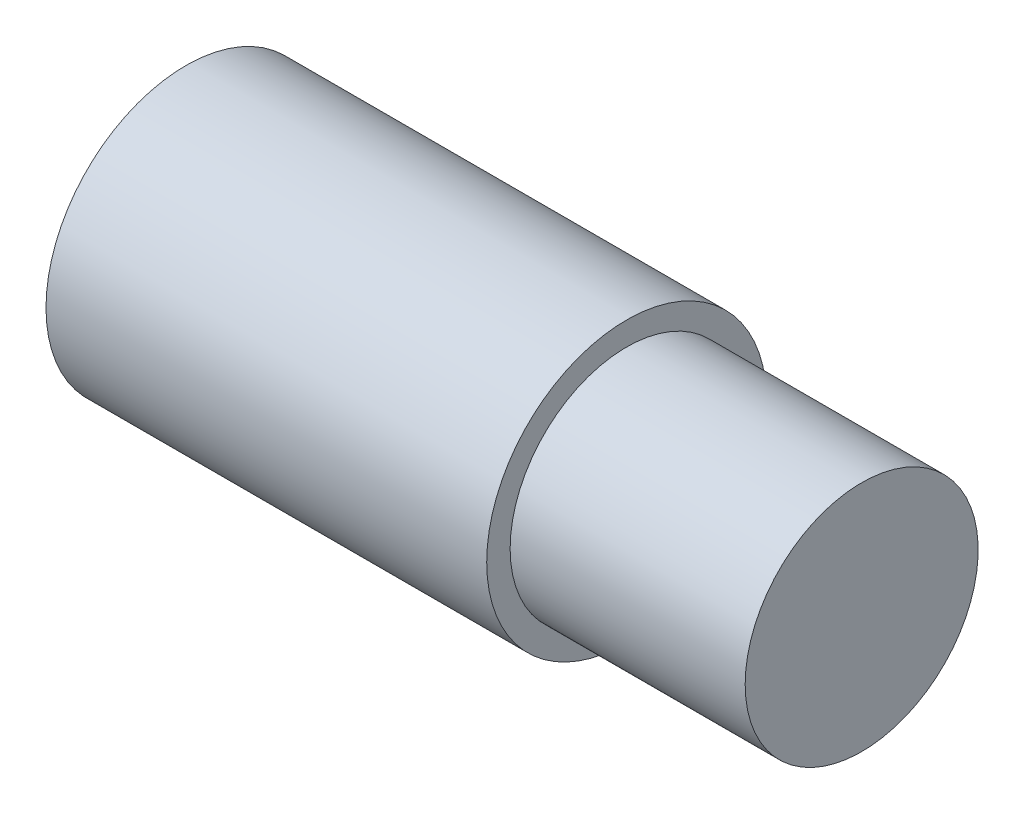
SolidWorks part; units mm, degrees
material "AISI 304"
ref_plane "Front Plane" through (0, 0, 0) normal (0, 0, 1) x (1, 0, 0)
ref_plane "Top Plane" through (0, 0, 0) normal (0, 1, 0) x (1, 0, 0)
ref_plane "Right Plane" through (0, 0, 0) normal (1, 0, 0) x (0, 0, -1)
sketch "Sketch1" plane through (0, 0, 0) normal (0, 0, 1) x (1, 0, 0)
  line L0 (0, 0) -> (0, 4.7625)
  line L1 (0, 4.7625) -> (15, 4.7625)
  line L2 (15, 4.7625) -> (15, 3.965)
  line L3 (15, 3.965) -> (23, 3.965)
  line L4 (23, 3.965) -> (23, 0)
  line L5 (23, 0) -> (0, 0)
  line L6 (-58.0552, 0) -> (-11.7734, 0) construction
  dimension "D1" = 9.525
  dimension "D2" = 7.93
  dimension "D3" = 23
  dimension "D4" = 8
revolve "Revolve1" add sketch "Sketch1" angle 360 about L6
